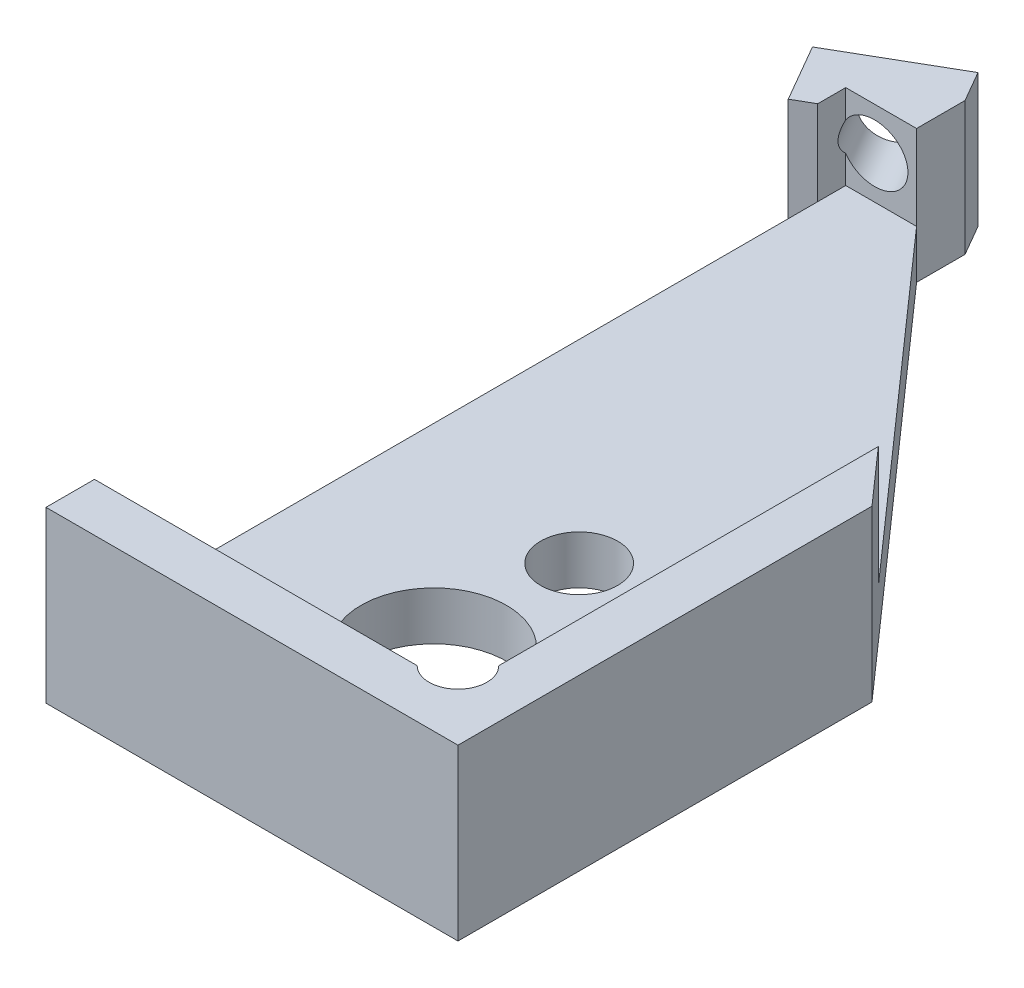
SolidWorks part; units mm, degrees
ref_plane "Front Plane" through (0, 0, 0) normal (0, 0, 1) x (1, 0, 0)
ref_plane "Top Plane" through (0, 0, 0) normal (0, 1, 0) x (1, 0, 0)
ref_plane "Right Plane" through (0, 0, 0) normal (1, 0, 0) x (0, 0, -1)
sketch "Sketch1" plane through (0, 0, 0) normal (0, 1, 0) x (1, 0, 0)
  line L7 (4.25, 8.75) -> (-4.25, 8.75)
  line L8 (4.25, 8.75) -> (4.25, -8.75)
  line L9 (4.25, -8.75) -> (-4.25, -8.75)
  line L10 (-4.25, 8.75) -> (-4.25, -8.75)
  line L11 (4.25, 8.75) -> (-4.25, -8.75) construction
  line L12 (4.25, -8.75) -> (-4.25, 8.75) construction
  point P0 (0, 0)
  point P6 (0, 0)
  dimension "D1" = 8.5
  dimension "D2" = 17.5
extrude "Boss-Extrude1" add sketch "Sketch1" along normal blind 3.5
sketch "Sketch2" plane through (0, 3.5, 0) normal (0, 1, 0) x (1, 0, 0)
  line L0 (-4.25, 8.75) -> (-4.25, -8.75) construction
  line L1 (3.25, 7.75) -> (-3.25, 7.75)
  line L2 (3.25, 7.75) -> (3.25, -7.75)
  line L3 (3.25, -7.75) -> (-3.25, -7.75)
  line L4 (-3.25, 7.75) -> (-3.25, -7.75)
  line L5 (3.25, 7.75) -> (-3.25, -7.75) construction
  line L6 (3.25, -7.75) -> (-3.25, 7.75) construction
  line L7 (4.25, 8.75) -> (-4.25, 8.75) construction
  point P0 (0, 0)
  dimension "D1" = 1
  dimension "D2" = 1
extrude "Cut-Extrude1" cut sketch "Sketch2" against normal offset from surface (2.5 mm away) 1 up to face at (0, 0, 0)
sketch "Sketch3" plane through (0, 1, 0) normal (0, 1, 0) x (1, 0, 0)
  line L0 (-3.25, -7.75) -> (3.25, -7.75) construction
  line L1 (3.25, -7.75) -> (3.25, 7.75) construction
  circle A0 centre (-0.25, -4.75) radius 1.5
  dimension "D1" = 3
  dimension "D2" = 3
  dimension "D3" = 3.5
extrude "GRIN Hole" cut sketch "Sketch3" against normal through all
sketch "Sketch6" plane through (0, 3.5, 0) normal (0, 1, 0) x (1, 0, 0)
  line L0 (3.25, -7.75) -> (3.25, 7.75) construction
  line L2 (-3.25, -7.75) -> (3.25, -7.75) construction
  line L3 (3.25, -7.3291) -> (2.8291, -7.3291) construction
  line L4 (2.8291, -7.3291) -> (2.8291, -7.75) construction
  circle A3 centre (2.8291, -7.3291) radius 0.5953
  dimension "D1" = 1.1906
extrude "Corner divot" cut sketch "Sketch6" against normal up to surface (2.5 mm away) up to face at (-0.25, 1, 6.25)
sketch "Sketch7" plane through (0, 1, 0) normal (0, 1, 0) x (1, 0, 0)
  line L0 (1.625, -1.75) -> (-2.125, -1.75) construction
  line L1 (-2.125, -1.75) -> (-2.125, -6.5) construction
  line L2 (-2.125, -6.5) -> (1.625, -6.5) construction
  line L3 (1.625, -6.5) -> (1.625, -1.75) construction
  line L4 (-0.25, -1.75) -> (-0.25, -4.75) construction
  circle A0 centre (-0.25, -1.75) radius 0.7937
  circle A2 centre (-2.125, -6.5) radius 0.7938
  circle A3 centre (1.625, -6.5) radius 0.7938
  circle A4 centre (-0.25, -4.75) radius 1.5 construction
  dimension "D1" = 1.5875
  dimension "D2" = 3.75
  dimension "D3" = 3
  dimension "D4" = 1.75
extrude "Magnet Holes" cut sketch "Sketch7" against normal through all
sketch "Sketch9" plane through (0, 3.5, 0) normal (0, 1, 0) x (1, 0, 0)
  line L0 (-3.1539, 9.3829) -> (-5.3189, 8.1329)
  line L1 (-4.0219, 7.3043) -> (-4.6359, 6.9498)
  line L2 (-4.0219, 7.3043) -> (-3.0849, 7.8453)
  line L3 (-3.1539, 9.3829) -> (-2.4709, 8.1998)
  line L4 (3.25, -4.75) -> (-1.9462, 4.25) construction
  line L5 (3.25, -4.75) -> (-1.9462, -7.75) construction
  line L6 (-3.25, -7.75) -> (2.4081, -7.75) construction
  line L8 (-1.9462, -7.75) -> (-1.9462, 4.25) construction
  line L9 (-1.9462, 4.25) -> (3.25, 4.25) construction
  line L10 (3.25, -6.9081) -> (3.25, 7.75) construction
  line L11 (3.25, 4.25) -> (3.25, -4.75) construction
  line L12 (-1.9462, 3.709) -> (-1.0091, 4.25) construction
  line L13 (-1.9462, 3.709) -> (-4.0219, 7.3043) construction
  line L14 (-1.4776, 3.9795) -> (-3.5534, 7.5748) construction
  line L15 (-2.4709, 8.1998) -> (-3.0849, 7.8453)
  line L16 (-4.6359, 6.9498) -> (-5.3189, 8.1329)
  line L17 (-3.5534, 7.5748) -> (-4.2364, 8.7579) construction
  dimension "D1" = 6
  dimension "D2" = 9
  dimension "D3" = 1.082
  dimension "D4" = 2.5
extrude "Boss-Extrude2" add sketch "Sketch9" against normal up to surface (3.5 mm away) up to face at (1.625, 0, 7.2938)
sketch "Sketch14" plane through (0, 3.5, 0) normal (0, 1, 0) x (1, 0, 0)
  line L1 (-6.2326, 5.1835) -> (-0.2674, 5.1835)
  line L2 (-6.2326, 5.1835) -> (-6.2326, 10.3165)
  line L3 (-6.2326, 10.3165) -> (-0.2674, 10.3165)
  line L4 (-0.2674, 5.1835) -> (-0.2674, 10.3165)
  line L5 (-6.2326, 5.1835) -> (-0.2674, 10.3165) construction
  line L6 (-6.2326, 10.3165) -> (-0.2674, 5.1835) construction
  point P0 (-3.25, 7.75)
extrude "Set Screw Extension" cut sketch "Sketch14" against normal blind 0.75
sketch "Sketch10" plane through (-4.8514, 0, -8.4028) normal (-0.5, 0, -0.866) x (-0.866, 0, 0.5)
  line L0 (-0.7101, 1) -> (-0.7101, 1.875) construction
  line L1 (-1.9601, 2.75) -> (0.5399, 2.75) construction
  line L2 (-0.7101, 1.875) -> (-0.7101, 2.75) construction
  line L4 (-0.7101, 1) -> (-0.7101, 0) construction
  line L5 (-1.9601, 0) -> (0.5399, 0) construction
  dimension "D1" = 1
hole_wizard "Tap Drill for #0-80 Tap1" positions "Sketch12" profile "Sketch11" hole size "#0-80" standard "ANSI Inch"
sketch "Sketch12" plane through (-4.8514, 0, -8.4028) normal (-0.5, 0, -0.866) x (-0.866, 0, 0.5)
  point P0 (-0.7101, 1.875)
sketch "Sketch11" plane through (-4.2364, 1.875, -8.7579) normal (0, 1, 0) x (-0.866, 0, 0.5)
  line L0 (0, 0) -> (0, 7.4679)
  line L1 (0, 7.4679) -> (0.5956, 7.11)
  line L2 (0.5956, 7.11) -> (0.5956, 0)
  line L5 (0.5956, 0) -> (0, 0)
  line L10 (0, 7.4679) -> (-0.5956, 7.11) construction
  line L11 (0, -6.35) -> (0, 107.95) construction
  dimension "Hole Dia." = 1.1913
  dimension "Hole Depth" = 7.11
  dimension "Drill Angle" = 118
sketch "Sketch15" plane through (0, 0, 0) normal (0, 1, 0) x (1, 0, 0)
  line L2 (-2.7885, 9.3132) -> (-2.7885, 7.75)
  line L4 (3.25, 7.75) -> (-3.25, 7.75) construction
  line L5 (-2.7885, 9.3132) -> (4.25, 9.3132)
  line L6 (4.25, 9.3132) -> (4.25, -0.2086)
  line L7 (-2.7885, 7.75) -> (4.25, -0.2086)
  line L8 (4.25, -8.75) -> (4.25, 8.75) construction
extrude "Diagonal Cut" cut sketch "Sketch15" along normal blind 5
sketch "Sketch16" plane through (0, 1, 0) normal (0, 1, 0) x (1, 0, 0)
  line L0 (-4.25, -7.75) -> (-4.25, 7.75)
  line L1 (-4.25, 7.75) -> (-3.25, 7.75)
  line L2 (-3.25, 7.75) -> (-3.25, -7.75)
  line L3 (-3.25, -7.75) -> (-4.25, -7.75)
  line L6 (-4.25, 7.1726) -> (-4.25, -8.75) construction
extrude "Vertical Cut" cut sketch "Sketch16" along normal blind 3
